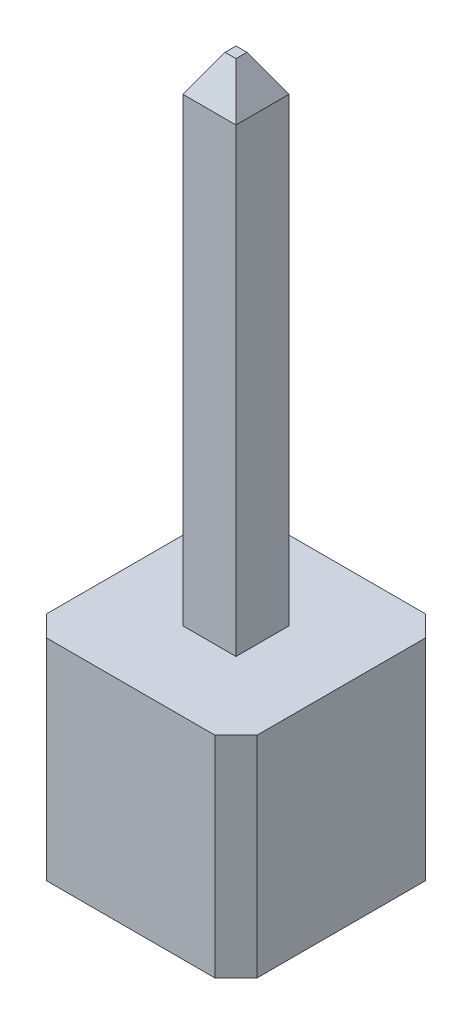
SolidWorks part; units mm, degrees
ref_plane "Front Plane" through (0, 0, 0) normal (0, 0, 1) x (1, 0, 0)
ref_plane "Top Plane" through (0, 0, 0) normal (0, 1, 0) x (1, 0, 0)
ref_plane "Right Plane" through (0, 0, 0) normal (1, 0, 0) x (0, 0, -1)
sketch "Sketch1" plane through (0, 0, 0) normal (0, 1, 0) x (1, 0, 0)
  line L1 (1.27, -1.27) -> (-1.27, -1.27)
  line L2 (1.27, -1.27) -> (1.27, 1.27)
  line L3 (1.27, 1.27) -> (-1.27, 1.27)
  line L4 (-1.27, -1.27) -> (-1.27, 1.27)
  line L5 (1.27, -1.27) -> (-1.27, 1.27) construction
  line L6 (1.27, 1.27) -> (-1.27, -1.27) construction
  line L7 (0.32, -0.32) -> (-0.32, -0.32)
  line L8 (0.32, -0.32) -> (0.32, 0.32)
  line L9 (0.32, 0.32) -> (-0.32, 0.32)
  line L10 (-0.32, -0.32) -> (-0.32, 0.32)
  line L11 (0.32, -0.32) -> (-0.32, 0.32) construction
  line L12 (0.32, 0.32) -> (-0.32, -0.32) construction
  point P0 (0, 0)
  point P6 (0, 0)
  point P11 (0, 0)
  dimension "D1" = 2.54
  dimension "D2" = 2.54
  dimension "D3" = 0.64
extrude "Boss-Extrude1" add sketch "Sketch1" along normal blind 2.54
chamfer "Chamfer1" distance 0.254 4 edges at (-1.27, 1.27, 1.27) (-1.27, 1.27, -1.27) (1.27, 1.27, -1.27) (1.27, 1.27, 1.27)
sketch "Sketch2" plane through (0, 0, 0) normal (0, -1, 0) x (1, 0, 0)
  line L1 (-0.32, 0.32) -> (0.32, 0.32)
  line L2 (-0.32, 0.32) -> (-0.32, -0.32)
  line L3 (-0.32, -0.32) -> (0.32, -0.32)
  line L4 (0.32, 0.32) -> (0.32, -0.32)
extrude "Boss-Extrude2" add sketch "Sketch2" against normal blind 8.54 separate body
chamfer "Chamfer2" distance 0.254 angle 60 4 edges at (0, 8.54, -0.32) (0.32, 8.54, 0) (0, 8.54, 0.32) (-0.32, 8.54, 0)
